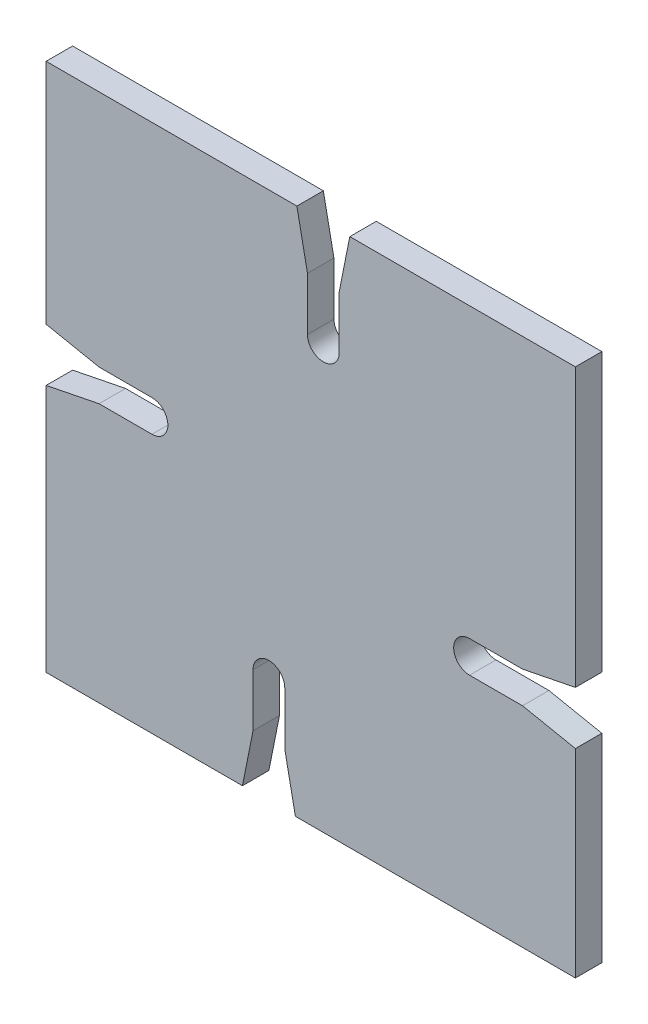
SolidWorks part; units mm, degrees
ref_plane "Vorderansicht" through (0, 0, 0) normal (0, 0, 1) x (1, 0, 0)
ref_plane "Draufsicht" through (0, 0, 0) normal (0, 1, 0) x (1, 0, 0)
ref_plane "Seitenansicht" through (0, 0, 0) normal (1, 0, 0) x (0, 0, -1)
sketch "Skizze1" plane through (0, 0, 0) normal (0, 0, 1) x (1, 0, 0)
  line L1 (0, 0) -> (100, 0)
  line L2 (0, 0) -> (0, 100)
  line L3 (0, 100) -> (100, 100)
  line L4 (100, 0) -> (100, 100)
  dimension "D1" = 100
  dimension "D2" = 100
extrude "Aufsatz-Linear austragen1" add sketch "Skizze1" along normal blind 5
sketch "Skizze2" plane through (61.5416, 22.6757, 5) normal (0, 0, 1) x (1, 0, 0)
  line L0 (-24.4509, -22.6757) -> (-22.4509, -12.6757)
  line L1 (-61.5416, -22.6757) -> (38.4584, -22.6757) construction
  line L2 (-22.4509, -12.6757) -> (-22.4509, -2.6757)
  line L3 (-16.4509, -2.6757) -> (-16.4509, -12.6757)
  line L4 (-16.4509, -12.6757) -> (-14.4509, -22.6757)
  line L5 (-14.4509, -22.6757) -> (-24.4509, -22.6757)
  line L6 (-19.4509, -2.6757) -> (-19.4509, -19.1265) construction
  arc A0 (-22.4509, -2.6757) -> (-16.4509, -2.6757) centre (-19.4509, -2.6757) cw
  dimension "D1" = 20
  dimension "D2" = 6
  dimension "D3" = 10
  dimension "D4" = 10
extrude "Schnitt-Linear austragen1" cut sketch "Skizze2" against normal up to next
other "Blechschlitz6mm<1>"
sketch "Skizze24" plane through (44.0559, 74.4667, 5) normal (0, 0, 1) x (1, 0, 0)
  line L0 (-44.0559, -17.5) -> (-34.0559, -19.5)
  line L1 (-44.0559, 25.5333) -> (-44.0559, -74.4667) construction
  line L2 (-34.0559, -19.5) -> (-24.0559, -19.5)
  line L3 (-24.0559, -25.5) -> (-34.0559, -25.5)
  line L4 (-34.0559, -25.5) -> (-44.0559, -27.5)
  line L5 (-44.0559, -27.5) -> (-44.0559, -17.5)
  line L6 (-24.0559, -22.5) -> (-44.0559, -22.5) construction
  arc A0 (-24.0559, -19.5) -> (-24.0559, -25.5) centre (-24.0559, -22.5) cw
  dimension "D1" = 20
  dimension "D2" = 6
  dimension "D3" = 10
  dimension "D4" = 10
extrude "Schnitt-Linear austragen14" cut sketch "Skizze24" against normal up to next
other "Blechschlitz6mm<2>"
sketch "Skizze25" plane through (81.6252, 83.3655, 5) normal (0, 0, 1) x (1, 0, 0)
  line L0 (-24.2476, 16.6345) -> (-26.2476, 6.6345)
  line L1 (18.3748, 16.6345) -> (-81.6252, 16.6345) construction
  line L2 (-26.2476, 6.6345) -> (-26.2476, -3.3655)
  line L3 (-32.2476, -3.3655) -> (-32.2476, 6.6345)
  line L4 (-32.2476, 6.6345) -> (-34.2476, 16.6345)
  line L5 (-34.2476, 16.6345) -> (-24.2476, 16.6345)
  line L6 (-29.2476, -3.3655) -> (-29.2476, 16.6345) construction
  arc A0 (-26.2476, -3.3655) -> (-32.2476, -3.3655) centre (-29.2476, -3.3655) cw
  dimension "D1" = 20
  dimension "D2" = 6
  dimension "D3" = 10
  dimension "D4" = 10
extrude "Schnitt-Linear austragen15" cut sketch "Skizze25" against normal up to next
other "Blechschlitz6mm<3>"
sketch "Skizze26" plane through (95.8704, 55.0451, 5) normal (0, 0, 1) x (1, 0, 0)
  line L0 (4.1296, -17.5) -> (-5.8704, -15.5)
  line L1 (4.1296, -55.0451) -> (4.1296, 44.9549) construction
  line L2 (-5.8704, -15.5) -> (-15.8704, -15.5)
  line L3 (-15.8704, -9.5) -> (-5.8704, -9.5)
  line L4 (-5.8704, -9.5) -> (4.1296, -7.5)
  line L5 (4.1296, -7.5) -> (4.1296, -17.5)
  line L6 (-15.8704, -12.5) -> (4.1296, -12.5) construction
  arc A0 (-15.8704, -15.5) -> (-15.8704, -9.5) centre (-15.8704, -12.5) cw
  dimension "D1" = 20
  dimension "D2" = 6
  dimension "D3" = 10
  dimension "D4" = 10
extrude "Schnitt-Linear austragen16" cut sketch "Skizze26" against normal up to next
other "Blechschlitz6mm<4>"
